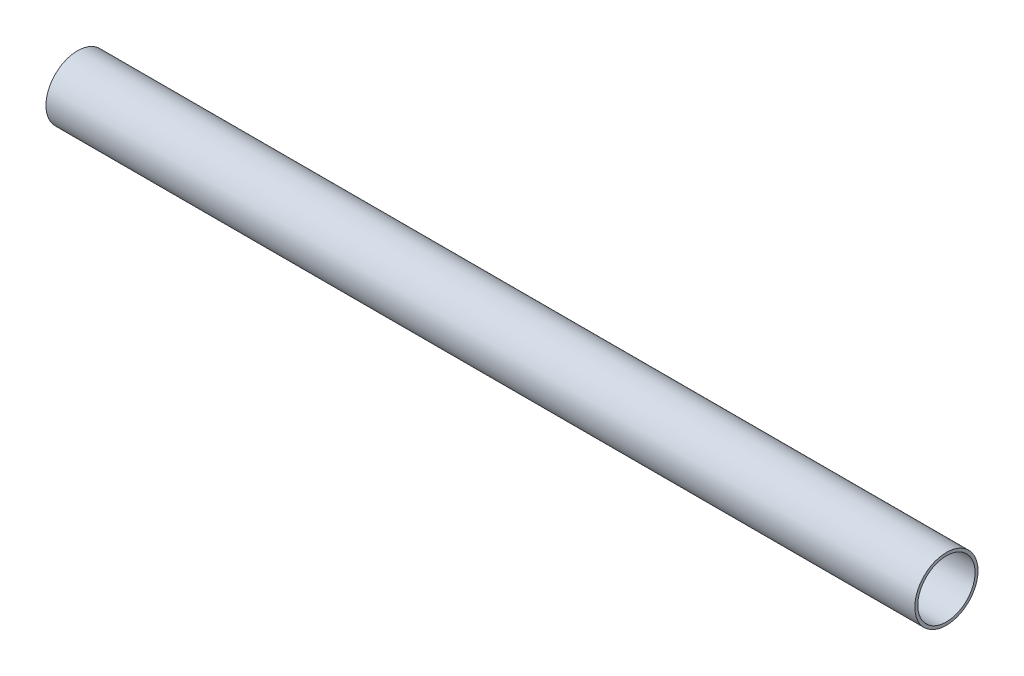
SolidWorks part; units mm, degrees
material "2024 Alloy"
ref_plane "Front Plane" through (0, 0, 0) normal (0, 0, 1) x (1, 0, 0)
ref_plane "Top Plane" through (0, 0, 0) normal (0, 1, 0) x (1, 0, 0)
ref_plane "Right Plane" through (0, 0, 0) normal (1, 0, 0) x (0, 0, -1)
sketch "Sketch1" plane through (0, 0, 0) normal (0, 0, 1) x (1, 0, 0)
  line L0 (0, 8) -> (0, 7.25)
  line L1 (0, 7.25) -> (220, 7.25)
  line L2 (220, 7.25) -> (220, 8)
  line L3 (220, 8) -> (0, 8)
  line L4 (0, 0) -> (220, 0) construction
revolve "Revolve1" add sketch "Sketch1" angle 360 about L4
